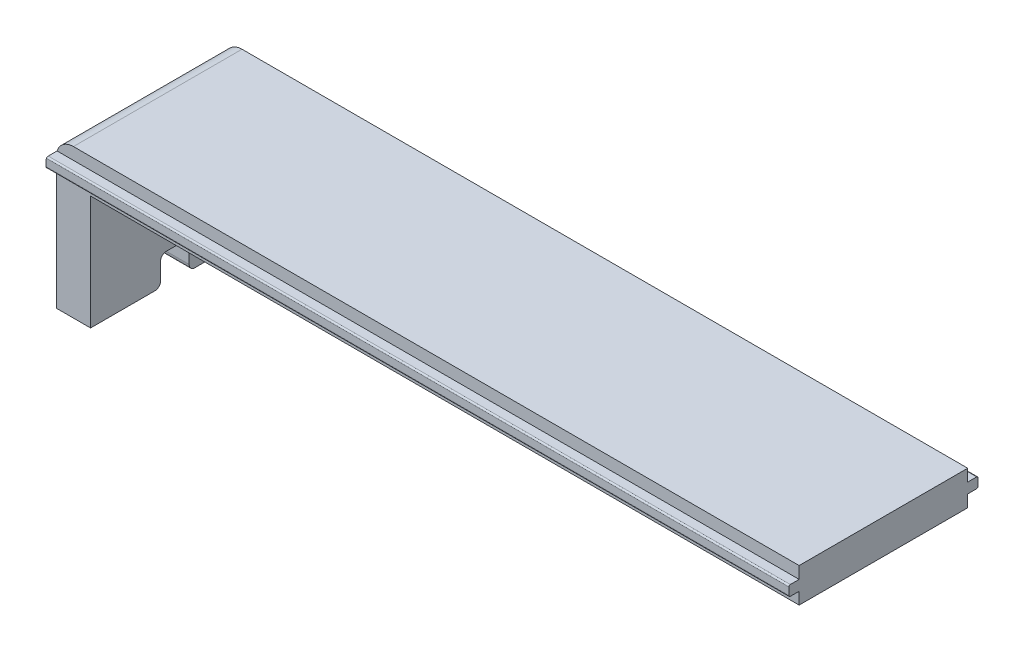
SolidWorks part; units mm, degrees
ref_plane "Front Plane" through (0, 0, 0) normal (0, 0, 1) x (1, 0, 0)
ref_plane "Top Plane" through (0, 0, 0) normal (0, 1, 0) x (1, 0, 0)
ref_plane "Right Plane" through (0, 0, 0) normal (1, 0, 0) x (0, 0, -1)
sketch "Sketch1" plane through (0, 0, 0) normal (0, 0, 1) x (1, 0, 0)
  line L0 (0, 0) -> (0, 26)
  line L1 (0, 26) -> (130, 26)
  line L2 (130, 26) -> (130, 20)
  line L3 (130, 20) -> (6, 20)
  line L4 (6, 20) -> (6, 0)
  line L5 (6, 0) -> (0, 0)
  dimension "D1" = 130
  dimension "D2" = 26
  dimension "D3" = 6
  dimension "D4" = 6
extrude "Boss-Extrude1" add sketch "Sketch1" along normal blind 29.5
sketch "Sketch2" plane through (0, 0, 0) normal (-1, 0, 0) x (0, 0, 1)
  line L0 (14.75, 26) -> (14.75, 0) construction
  line L1 (29.5, 26) -> (0, 26) construction
  line L2 (29.5, 0) -> (0, 0) construction
  line L4 (17.25, 0) -> (12.25, 0)
  line L5 (17.25, 0) -> (17.25, 5)
  line L6 (17.25, 5) -> (12.25, 5)
  line L7 (12.25, 0) -> (12.25, 5)
  point P10 (14.75, 5)
  dimension "D1" = 5
  dimension "D2" = 5
extrude "Cut-Extrude1" cut sketch "Sketch2" against normal up to next
sketch "Sketch3" plane through (0, 0, 0) normal (-1, 0, 0) x (0, 0, 1)
  line L0 (0, 26) -> (0, 0) construction
  line L1 (0, 23.9) -> (-1.8, 23.9)
  line L2 (0, 23.9) -> (0, 22.1)
  line L3 (0, 22.1) -> (-1.8, 22.1)
  line L4 (-1.8, 23.9) -> (-1.8, 22.1)
  line L5 (29.5, 26) -> (29.5, 0) construction
  line L6 (29.5, 23.9) -> (31.3, 23.9)
  line L7 (29.5, 23.9) -> (29.5, 22.1)
  line L8 (29.5, 22.1) -> (31.3, 22.1)
  line L9 (31.3, 23.9) -> (31.3, 22.1)
  line L10 (31.3, 23) -> (29.5, 23) construction
  line L11 (-1.8, 23) -> (0, 23) construction
  line L12 (29.5, 26) -> (0, 26) construction
  dimension "D1" = 1.8
  dimension "D2" = 1.8
  dimension "D3" = 3
  dimension "D4" = 3
extrude "Boss-Extrude2" add sketch "Sketch3" against normal up to surface (130 mm away) up to face at (130, 23, 14.75)
fillet "Fillet1" radius 3 1 edges at (0, 26, 14.75)
fillet "Fillet2" radius 1 7 edges at (0, 2.5, 12.25) (0, 5, 14.75) (0, 2.5, 17.25) (3, 0, 17.25) (3, 0, 12.25) (3, 5, 12.25) (3, 5, 17.25)
fillet "Fillet3" radius 0.25 4 edges at (65, 22.1, 31.3) (65.0691, 23.9, 31.3) (65, 22.1, -1.8) (65.0691, 23.9, -1.8)
